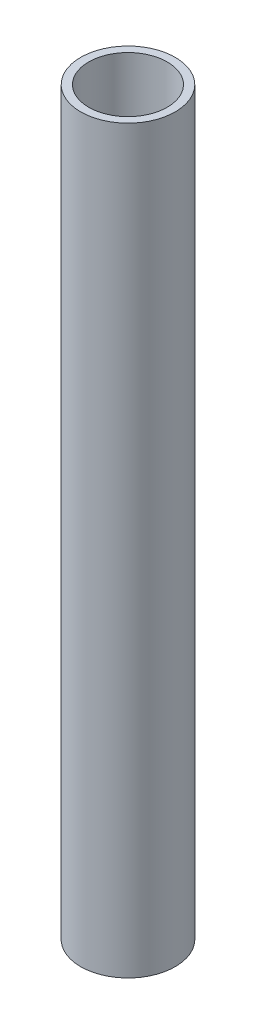
SolidWorks part; units mm, degrees
material "6061 Alloy"
ref_plane "Front Plane" through (0, 0, 0) normal (0, 0, 1) x (1, 0, 0)
ref_plane "Top Plane" through (0, 0, 0) normal (0, 1, 0) x (1, 0, 0)
ref_plane "Right Plane" through (0, 0, 0) normal (1, 0, 0) x (0, 0, -1)
sketch "Sketch1" plane through (0, 0, 0) normal (0, 1, 0) x (1, 0, 0)
  circle A0 centre (0, 0) radius 21.082
  circle A1 centre (0, 0) radius 17.526
  dimension "D1" = 42.164
  dimension "D2" = 35.052
extrude "Boss-Extrude1" add sketch "Sketch1" along normal blind 330.2
